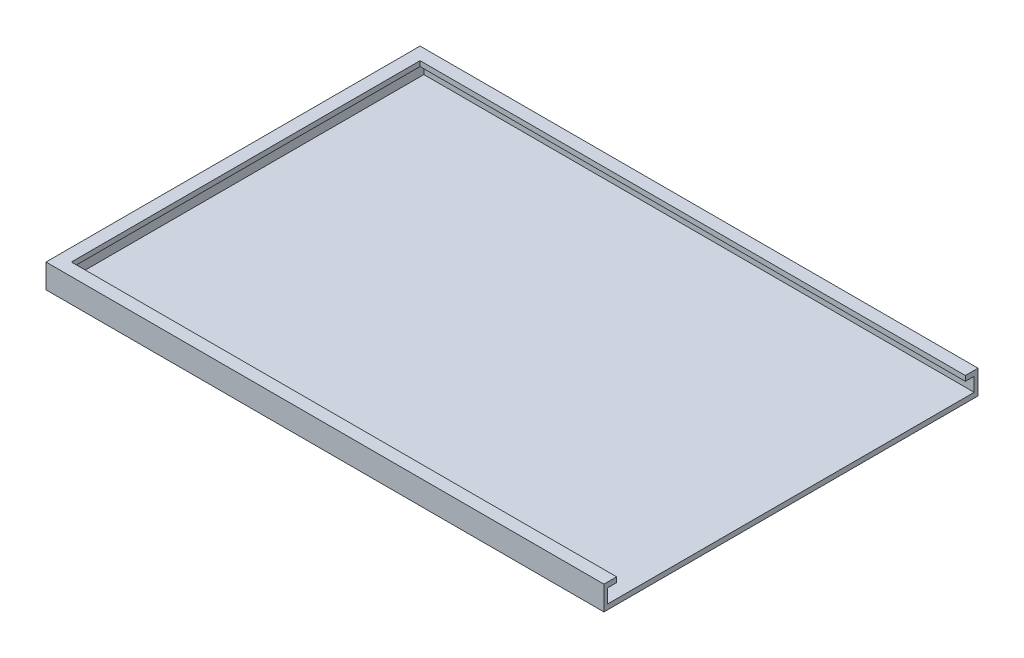
SolidWorks part; units mm, degrees
ref_plane "Спереди" through (0, 0, 0) normal (0, 0, 1) x (1, 0, 0)
ref_plane "Сверху" through (0, 0, 0) normal (0, 1, 0) x (1, 0, 0)
ref_plane "Справа" through (0, 0, 0) normal (1, 0, 0) x (0, 0, -1)
other "Configuration Table"
sketch "Эскиз1" plane through (0, 0, 0) normal (0, 1, 0) x (1, 0, 0)
  line L1 (-43, -27.5) -> (43, -27.5)
  line L2 (-43, -27.5) -> (-43, 27.5)
  line L3 (-43, 27.5) -> (43, 27.5)
  line L4 (43, -27.5) -> (43, 27.5)
  line L5 (0, 27.5) -> (0, -27.5) construction
  line L6 (-43, 0) -> (43, 0) construction
  point P0 (0, 0)
  dimension "D1" = 86
  dimension "D2" = 55
extrude "низ" add sketch "Эскиз1" along normal blind 0.8
sketch "Эскиз2" plane through (0, 0, -27.5) normal (0, 0, -1) x (-1, 0, 0)
  line L0 (-43, 0.8) -> (43, 0.8) construction
  line L1 (-43, 0) -> (45, 0)
  line L2 (-43, 0) -> (-43, 3.8)
  line L3 (-43, 3.8) -> (45, 3.8)
  line L4 (45, 0) -> (45, 3.8)
  line L5 (1, 3.8) -> (1, 0) construction
  line L6 (-43, 1.9) -> (45, 1.9) construction
  line L7 (43, 0.8) -> (43, 0) construction
  point P896 (1, 1.9)
  dimension "D1" = 3
  dimension "D2" = 2
extrude "Бобышка-Вытянуть1" add sketch "Эскиз2" along normal blind 2
sketch "Эскиз3" plane through (0, 0, -27.5) normal (0, 0, 1) x (1, 0, 0)
  line L0 (-45, 0) -> (-45, 3.8) construction
  line L1 (43, 0.8) -> (-44.2, 0.8)
  line L2 (43, 0.8) -> (43, 3)
  line L3 (43, 3) -> (-44.2, 3)
  line L4 (-44.2, 0.8) -> (-44.2, 3)
  line L5 (-0.6, 3) -> (-0.6, 0.8) construction
  line L6 (43, 1.9) -> (-44.2, 1.9) construction
  point P448 (-0.6, 1.9)
  dimension "D1" = 2.2
  dimension "D2" = 0.8
extrude "Вырез-Вытянуть1" cut sketch "Эскиз3" against normal blind 1.4
ref_plane "Плоскость2" through (0, 0, 0) normal (0, 0, 1) x (1, 0, 0)
mirror "Зеркальное отражение1" about plane through (0, 0, 0) normal (0, 0, 1) of "Вырез-Вытянуть1", "Бобышка-Вытянуть1"
sketch "Эскиз4" plane through (-43, 0, 0) normal (-1, 0, 0) x (0, 0, 1)
  line L1 (-29.5, 0) -> (29.5, 0)
  line L2 (-29.5, 0) -> (-29.5, 3.8)
  line L3 (-29.5, 3.8) -> (29.5, 3.8)
  line L4 (29.5, 0) -> (29.5, 3.8)
  line L5 (0, 3.8) -> (0, 0) construction
  line L6 (-29.5, 1.9) -> (29.5, 1.9) construction
  point P308 (0, 1.9)
extrude "Бобышка-Вытянуть2" add sketch "Эскиз4" along normal blind 2
sketch "Эскиз5" plane through (-43, 0, 0) normal (1, 0, 0) x (0, 0, -1)
  line L1 (-28.9, 3) -> (28.9, 3)
  line L2 (-28.9, 3) -> (-28.9, 0.8)
  line L3 (-28.9, 0.8) -> (28.9, 0.8)
  line L4 (28.9, 3) -> (28.9, 0.8)
  line L5 (0, 0.8) -> (0, 3) construction
  line L6 (-28.9, 1.9) -> (28.9, 1.9) construction
  point P352 (0, 1.9)
extrude "Вырез-Вытянуть2" cut sketch "Эскиз5" against normal blind 0.8
